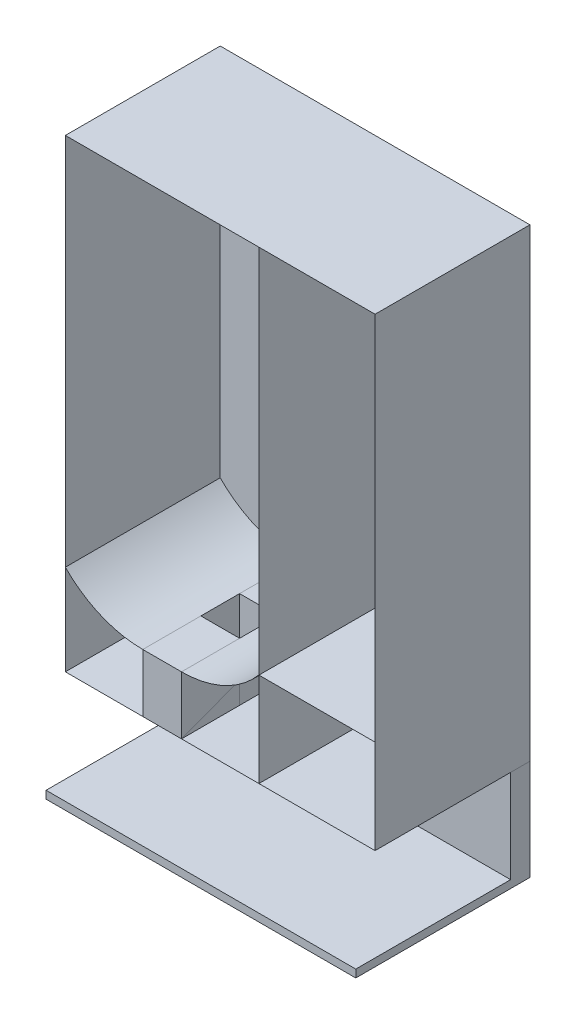
SolidWorks part; units mm, degrees
other "Markup1"
sketch "Sketch14"
ref_plane "Front Plane" through (0, 0, 0) normal (0, 0, 1) x (1, 0, 0)
ref_plane "Top Plane" through (0, 0, 0) normal (0, 1, 0) x (1, 0, 0)
ref_plane "Right Plane" through (0, 0, 0) normal (1, 0, 0) x (0, 0, -1)
sketch "Sketch1" plane through (0, 0, 0) normal (0, 0, 1) x (1, 0, 0)
  line L1 (-200, -300) -> (200, -300)
  line L2 (-200, -300) -> (-200, 300)
  line L3 (-200, 300) -> (200, 300)
  line L4 (200, -300) -> (200, 300)
  line L5 (0, 300) -> (0, -300) construction
  line L6 (-200, 0) -> (200, 0) construction
  point P0 (0, 0)
  dimension "D1" = 600
  dimension "D2" = 400
surface "Surface-Extrude1" sketch "Sketch1" parameters "D1"=200
sketch "Sketch2" plane through (200, 0, 0) normal (1, 0, 0) x (0, 0, -1)
  line L0 (0, 300) -> (0, -300)
surface "Surface-Extrude2" sketch "Sketch2" parameters "D1"=400
sketch "Sketch3" plane through (0, 0, 0) normal (0, 0, -1) x (-1, 0, 0)
  line L1 (-50, 300) -> (-50, -300)
  line L2 (200, 300) -> (-200, 300) construction
  line L3 (-200, -300) -> (200, -300) construction
  line L4 (-200, 300) -> (-200, -300) construction
  dimension "D1" = 150
surface "Surface-Extrude3" sketch "Sketch3" parameters "D1"=200
sketch "Sketch4" plane through (0, -300, 0) normal (0, -1, 0) x (1, 0, 0)
  line L0 (-200, 0) -> (200, 0)
  line L1 (200, 0) -> (200, 24.9261)
  line L2 (200, 0) -> (200, 200) construction
  line L3 (200, 24.9261) -> (-200, 24.9261)
  line L4 (-200, 0) -> (-200, 200) construction
  line L5 (-200, 24.9261) -> (-200, 0)
extrude "Boss-Extrude1" add sketch "Sketch4" along normal blind 130
sketch "Sketch5" plane through (0, 0, 24.9261) normal (0, 0, 1) x (1, 0, 0)
  line L0 (-200, -430) -> (-200, -420)
  line L1 (-200, -430) -> (-200, -300) construction
  line L2 (-200, -420) -> (200, -420)
  line L3 (200, -430) -> (200, -300) construction
  line L4 (200, -420) -> (200, -430)
  line L5 (200, -430) -> (-200, -430) construction
  line L6 (200, -430) -> (-200, -430)
  dimension "D1" = 10
extrude "Boss-Extrude2" add sketch "Sketch5" along normal blind 200
sketch "Sketch11" plane through (0, 0, 0) normal (0, 0, -1) x (-1, 0, 0)
  line L0 (100, -300) -> (100, -225)
  line L1 (-200, -300) -> (200, -300) construction
  line L3 (50, -225) -> (50, -300)
  line L4 (-200, -300) -> (200, -300) construction
  line L5 (50, -300) -> (100, -300)
  line L6 (200, -300) -> (200, 300) construction
  line L7 (200, -300) -> (200, 300) construction
  line L9 (50, -300) -> (50, -225)
  arc A0 (100, -225) -> (200, -182.9755) centre (100, -85.0094) ccw
  arc A1 (50, -225) -> (-50, -178.4401) centre (50, -94.3316) cw
  dimension "D1" = 50
  dimension "D2" = 100
  dimension "D3" = 75
  dimension "D4" = 75
  dimension "D5" = 75
surface "Surface-Extrude4" sketch "Sketch11" parameters "D1"=200
sketch "Sketch12" plane through (0, -300, 0) normal (0, 1, 0) x (1, 0, 0)
  line L0 (-100, -125) -> (-50, -125)
  line L1 (-100, 0) -> (-100, -200) construction
  line L2 (-50, 0) -> (-50, -200) construction
  line L3 (-50, -125) -> (-50, -200)
  line L4 (-50, -200) -> (-100, -200)
  line L5 (-100, -200) -> (-100, -125)
  line L6 (-100, -75) -> (-50, -75)
  line L7 (-100, 0) -> (-100, -200) construction
  line L8 (-50, -200) -> (-50, 0) construction
  line L9 (-50, -75) -> (-50, 0)
  line L10 (-50, 0) -> (-100, 0)
  line L11 (-100, 0) -> (-100, -75)
  dimension "D1" = 75
  dimension "D2" = 75
extrude "Boss-Extrude3" add sketch "Sketch12" along normal blind 75
sketch "Sketch13" plane through (0, 0, 0) normal (0, 0, -1) x (-1, 0, 0)
  line L0 (-49.9253, -178.6598) -> (-200, -178.6598)
  line L1 (-200, 300) -> (-200, -300) construction
surface "Surface-Extrude5" sketch "Sketch13" parameters "D1"=200
